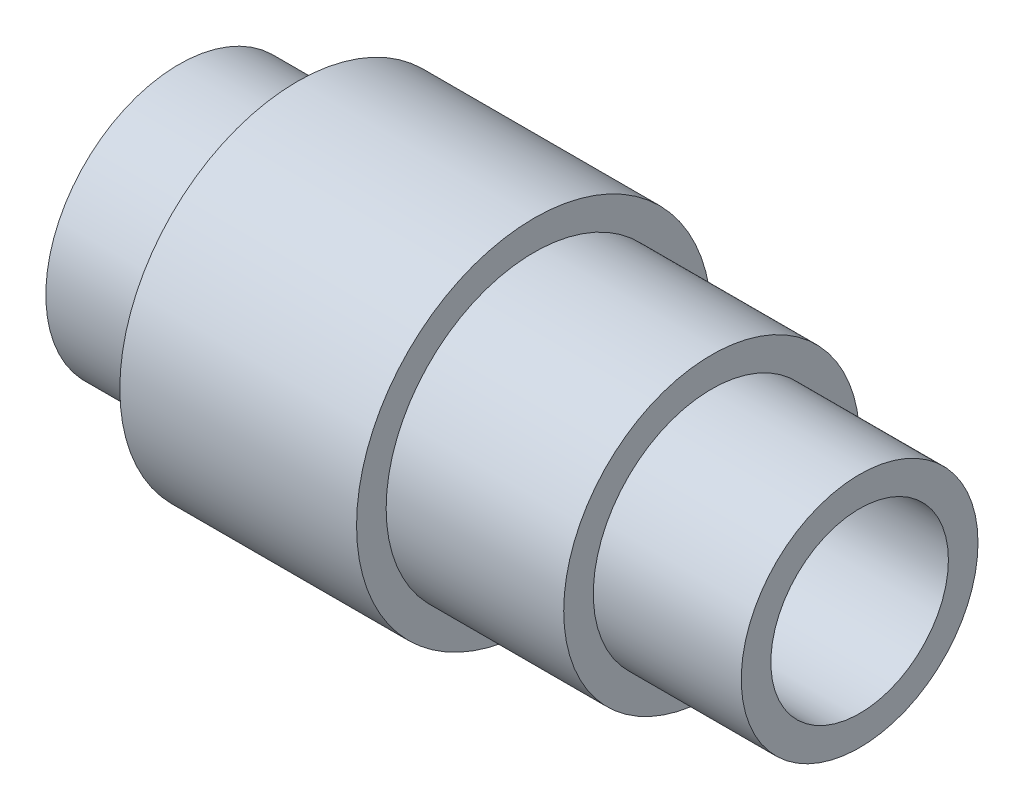
SolidWorks part; units mm, degrees
ref_plane "Front Plane" through (0, 0, 0) normal (0, 0, 1) x (1, 0, 0)
ref_plane "Top Plane" through (0, 0, 0) normal (0, 1, 0) x (1, 0, 0)
ref_plane "Right Plane" through (0, 0, 0) normal (1, 0, 0) x (0, 0, -1)
sketch "Sketch1" plane through (0, 0, 0) normal (1, 0, 0) x (0, 0, -1)
  circle A0 centre (0, 0) radius 22.5
  dimension "D1" = 45
extrude "Boss-Extrude1" add sketch "Sketch1" along normal blind 20
sketch "Sketch2" plane through (20, 0, 0) normal (1, 0, 0) x (0, 0, -1)
  circle A0 centre (0, 0) radius 30
  dimension "D1" = 60
extrude "Boss-Extrude2" add sketch "Sketch2" along normal blind 40
sketch "Sketch3" plane through (60, 0, 0) normal (1, 0, 0) x (0, 0, -1)
  circle A0 centre (0, 0) radius 25
  dimension "D1" = 50
extrude "Boss-Extrude3" add sketch "Sketch3" along normal blind 30
sketch "Sketch4" plane through (90, 0, 0) normal (1, 0, 0) x (0, 0, -1)
  circle A0 centre (0, 0) radius 20
  dimension "D1" = 40
extrude "Boss-Extrude4" add sketch "Sketch4" along normal blind 25
sketch "Sketch5" plane through (115, 0, 0) normal (1, 0, 0) x (0, 0, -1)
  circle A0 centre (0, 0) radius 15
  dimension "D1" = 30
extrude "Cut-Extrude1" cut sketch "Sketch5" against normal through all
